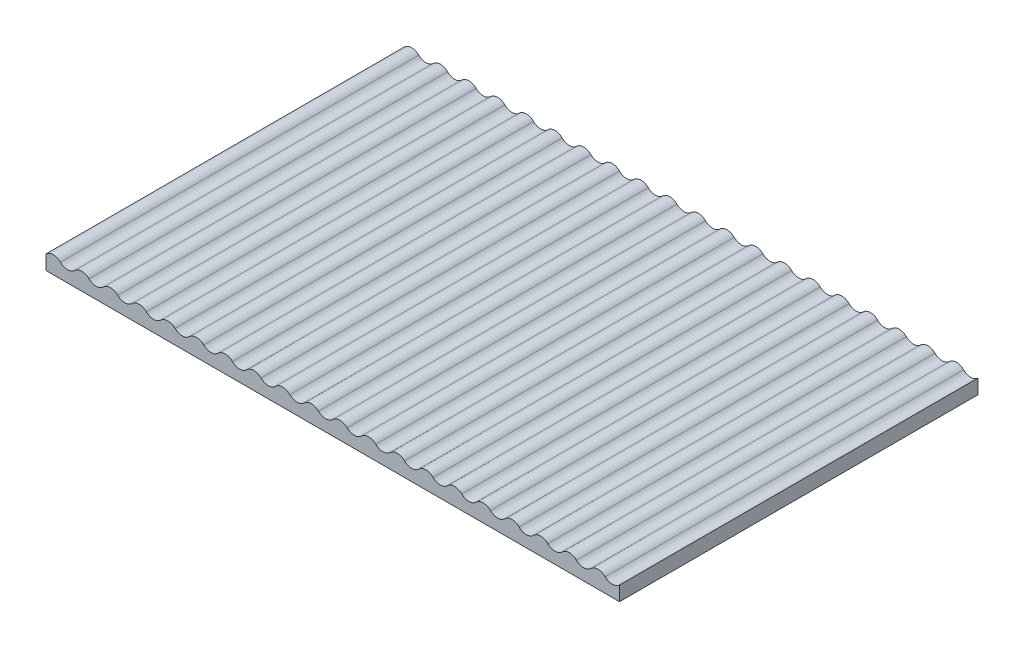
SolidWorks part; units mm, degrees
ref_plane "Front Plane" through (0, 0, 0) normal (0, 0, 1) x (1, 0, 0)
ref_plane "Top Plane" through (0, 0, 0) normal (0, 1, 0) x (1, 0, 0)
ref_plane "Right Plane" through (0, 0, 0) normal (1, 0, 0) x (0, 0, -1)
sketch "Sketch1" plane through (0, 0, 0) normal (0, 0, 1) x (1, 0, 0)
  line L1 (0, 0.0793) -> (0, -10)
  line L2 (0, -10) -> (400, -10)
  line L3 (400, -10) -> (400, 0.0793)
  arc A0 (0, 0.0793) -> (10, 0.0793) centre (5, -4.98) cw
  arc A1 (20, 0.0793) -> (30, 0.0793) centre (25, -4.98) cw
  arc A2 (40, 0.0793) -> (50, 0.0793) centre (45, -4.98) cw
  arc A3 (60, 0.0793) -> (70, 0.0793) centre (65, -4.98) cw
  arc A4 (80, 0.0793) -> (90, 0.0793) centre (85, -4.98) cw
  arc A5 (100, 0.0793) -> (110, 0.0793) centre (105, -4.98) cw
  arc A6 (120, 0.0793) -> (130, 0.0793) centre (125, -4.98) cw
  arc A7 (140, 0.0793) -> (150, 0.0793) centre (145, -4.98) cw
  arc A8 (160, 0.0793) -> (170, 0.0793) centre (165, -4.98) cw
  arc A9 (180, 0.0793) -> (190, 0.0793) centre (185, -4.98) cw
  arc A10 (200, 0.0793) -> (210, 0.0793) centre (205, -4.98) cw
  arc A11 (220, 0.0793) -> (230, 0.0793) centre (225, -4.98) cw
  arc A12 (240, 0.0793) -> (250, 0.0793) centre (245, -4.98) cw
  arc A13 (260, 0.0793) -> (270, 0.0793) centre (265, -4.98) cw
  arc A14 (280, 0.0793) -> (290, 0.0793) centre (285, -4.98) cw
  arc A15 (300, 0.0793) -> (310, 0.0793) centre (305, -4.98) cw
  arc A16 (320, 0.0793) -> (330, 0.0793) centre (325, -4.98) cw
  arc A17 (340, 0.0793) -> (350, 0.0793) centre (345, -4.98) cw
  arc A18 (360, 0.0793) -> (370, 0.0793) centre (365, -4.98) cw
  arc A19 (380, 0.0793) -> (390, 0.0793) centre (385, -4.98) cw
  arc A20 (10, 0.0793) -> (20, 0.0793) centre (15, 5.1386) ccw
  arc A21 (30, 0.0793) -> (40, 0.0793) centre (35, 5.1386) ccw
  arc A22 (50, 0.0793) -> (60, 0.0793) centre (55, 5.1386) ccw
  arc A23 (70, 0.0793) -> (80, 0.0793) centre (75, 5.1386) ccw
  arc A24 (90, 0.0793) -> (100, 0.0793) centre (95, 5.1386) ccw
  arc A25 (110, 0.0793) -> (120, 0.0793) centre (115, 5.1386) ccw
  arc A26 (130, 0.0793) -> (140, 0.0793) centre (135, 5.1386) ccw
  arc A27 (150, 0.0793) -> (160, 0.0793) centre (155, 5.1386) ccw
  arc A28 (170, 0.0793) -> (180, 0.0793) centre (175, 5.1386) ccw
  arc A29 (190, 0.0793) -> (200, 0.0793) centre (195, 5.1386) ccw
  arc A30 (210, 0.0793) -> (220, 0.0793) centre (215, 5.1386) ccw
  arc A31 (230, 0.0793) -> (240, 0.0793) centre (235, 5.1386) ccw
  arc A32 (250, 0.0793) -> (260, 0.0793) centre (255, 5.1386) ccw
  arc A33 (270, 0.0793) -> (280, 0.0793) centre (275, 5.1386) ccw
  arc A34 (290, 0.0793) -> (300, 0.0793) centre (295, 5.1386) ccw
  arc A35 (310, 0.0793) -> (320, 0.0793) centre (315, 5.1386) ccw
  arc A36 (330, 0.0793) -> (340, 0.0793) centre (335, 5.1386) ccw
  arc A37 (350, 0.0793) -> (360, 0.0793) centre (355, 5.1386) ccw
  arc A38 (370, 0.0793) -> (380, 0.0793) centre (375, 5.1386) ccw
  arc A39 (390, 0.0793) -> (400, 0.0793) centre (395, 5.1386) ccw
  dimension "D1" = 10
  dimension "D3" = 20
  dimension "D2" = 20
extrude "Boss-Extrude1" add sketch "Sketch1" against normal blind 250
